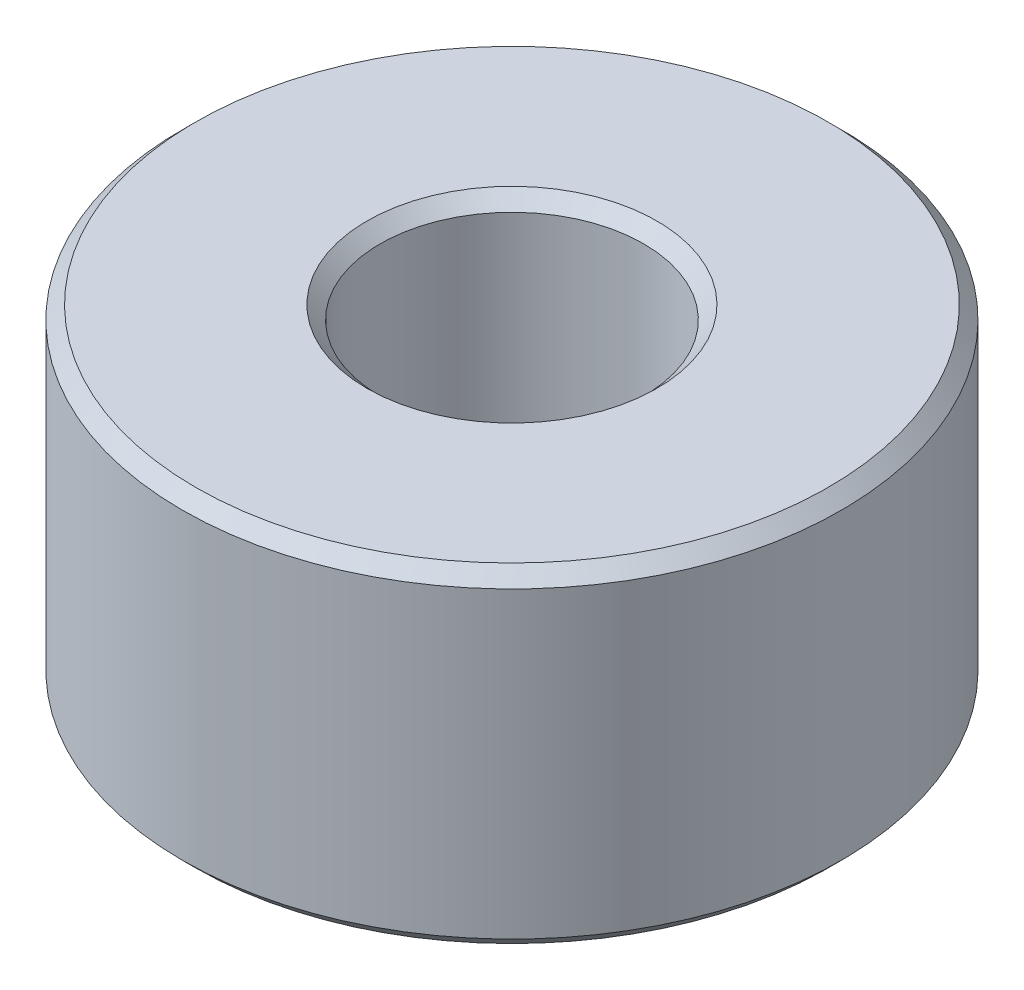
SolidWorks part; units mm, degrees
material "AISI 316 退火不锈钢条 (SS)"
ref_plane "前视基准面" through (0, 0, 0) normal (0, 0, 1) x (1, 0, 0)
ref_plane "上视基准面" through (0, 0, 0) normal (0, 1, 0) x (1, 0, 0)
ref_plane "右视基准面" through (0, 0, 0) normal (1, 0, 0) x (0, 0, -1)
sketch "草图1" plane through (0, 0, 0) normal (0, 1, 0) x (1, 0, 0)
  circle A0 centre (0, 0) radius 1
  circle A1 centre (0, 0) radius 2.5
  dimension "D1" = 2
  dimension "D2" = 5
extrude "凸台-拉伸1" add sketch "草图1" along normal blind 2.5
chamfer "倒角1" distance 0.1 angle 45 4 edges at (0, 0, 1) (0, 0, 2.5) (0, 2.5, 2.5) (0, 2.5, 1)
